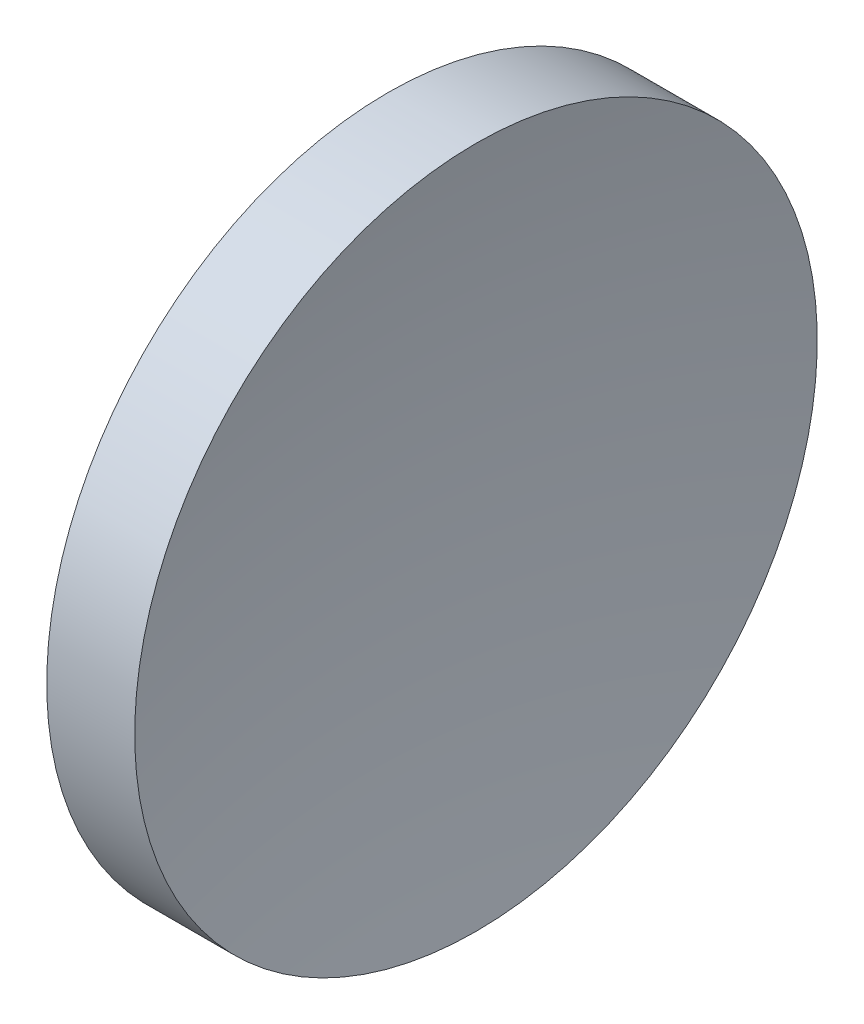
SolidWorks part; units mm, degrees
ref_plane "前视基准面" through (0, 0, 0) normal (0, 0, 1) x (1, 0, 0)
ref_plane "上视基准面" through (0, 0, 0) normal (0, 1, 0) x (1, 0, 0)
ref_plane "右视基准面" through (0, 0, 0) normal (1, 0, 0) x (0, 0, -1)
sketch "草图1" plane through (0, 0, 0) normal (0, 0, 1) x (1, 0, 0)
  line L0 (55.0074, 32.5787) -> (69.3049, 32.5787) construction
  line L1 (57.3582, 32.5787) -> (57.3582, 45.0787)
  line L2 (59.3582, 32.5787) -> (57.3582, 32.5787)
  line L3 (57.3582, 45.0787) -> (60.5805, 45.0787)
  arc A0 (60.5805, 45.0787) -> (59.3582, 32.5787) centre (123.9082, 32.5766) ccw
  dimension "D3" = 64.55
  dimension "D1" = 3.2223
  dimension "D2" = 12.5
revolve "旋转1" add sketch "草图1" angle 360 about L0
